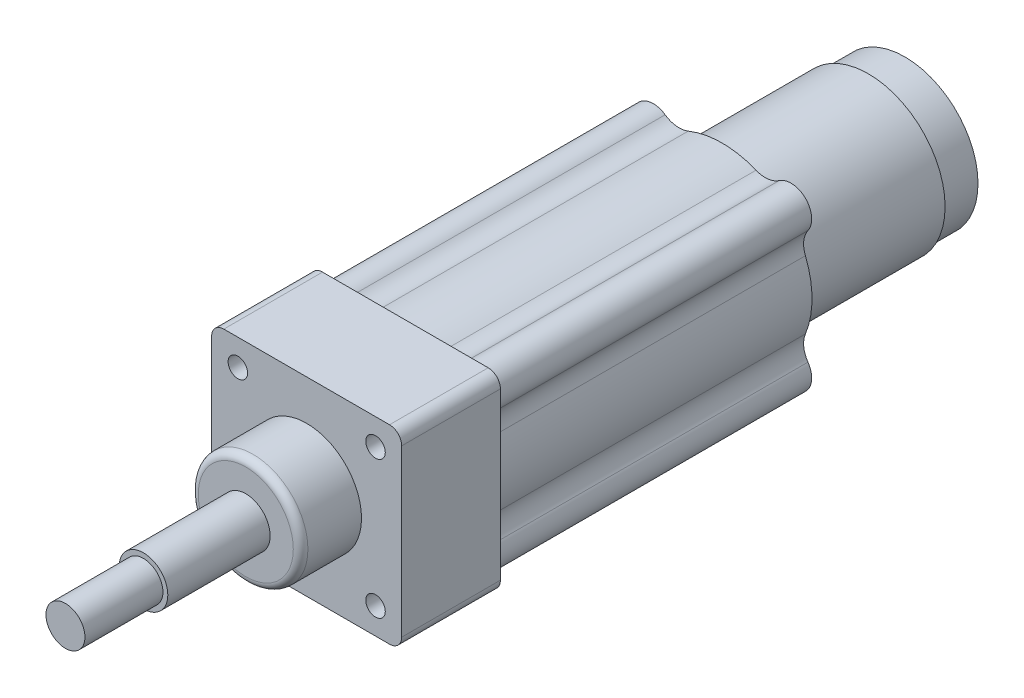
SolidWorks part; units mm, degrees
ref_plane "Alzado" through (0, 0, 0) normal (0, 0, 1) x (1, 0, 0)
ref_plane "Planta" through (0, 0, 0) normal (0, 1, 0) x (1, 0, 0)
ref_plane "Vista lateral" through (0, 0, 0) normal (1, 0, 0) x (0, 0, -1)
sketch "Croquis1" plane through (0, 0, 0) normal (0, 0, 1) x (1, 0, 0)
  line L1 (-34, -39) -> (34, -39)
  line L2 (-39, -34) -> (-39, 34)
  line L3 (-34, 39) -> (34, 39)
  line L4 (39, -34) -> (39, 34)
  line L5 (-39, -39) -> (39, 39) construction
  line L6 (-39, 39) -> (39, -39) construction
  arc A0 (34, -39) -> (39, -34) centre (34, -34) ccw
  arc A1 (-34, -39) -> (-39, -34) centre (-34, -34) cw
  arc A2 (-39, 34) -> (-34, 39) centre (-34, 34) cw
  arc A3 (34, 39) -> (39, 34) centre (34, 34) cw
  point P0 (0, 0)
  dimension "D3" = 5
  dimension "D1" = 78
  dimension "D2" = 78
extrude "Saliente-Extruir1" add sketch "Croquis1" against normal blind 40.5
sketch "Croquis2" plane through (0, 0, 0) normal (0, 0, 1) x (1, 0, 0)
  circle A0 centre (0, 0) radius 36.8862
extrude "Saliente-Extruir2" add sketch "Croquis2" against normal blind 170.5
sketch "Croquis3" plane through (0, 0, 0) normal (0, 0, 1) x (1, 0, 0)
  circle A0 centre (0, 0) radius 31.5
  dimension "D1" = 63
extrude "Saliente-Extruir3" add sketch "Croquis3" against normal blind 230.5
sketch "Croquis4" plane through (0, 0, -230.5) normal (0, 0, -1) x (-1, 0, 0)
  circle A0 centre (0, 0) radius 30
  dimension "D1" = 60
extrude "Saliente-Extruir4" add sketch "Croquis4" along normal blind 15
sketch "Croquis5" plane through (0, 0, 0) normal (0, 0, 1) x (1, 0, 0)
  line L1 (-28.25, -28.25) -> (28.25, -28.25) construction
  line L2 (-28.25, -28.25) -> (-28.25, 28.25) construction
  line L3 (-28.25, 28.25) -> (28.25, 28.25) construction
  line L4 (28.25, -28.25) -> (28.25, 28.25) construction
  line L5 (-28.25, -28.25) -> (28.25, 28.25) construction
  line L6 (-28.25, 28.25) -> (28.25, -28.25) construction
  circle A0 centre (28.25, 28.25) radius 8.5
  circle A1 centre (28.25, -28.25) radius 8.5
  circle A2 centre (-28.25, -28.25) radius 8.5
  circle A3 centre (-28.25, 28.25) radius 8.5
  point P8 (0, 0)
  dimension "D3" = 17
  dimension "D1" = 56.5
  dimension "D2" = 56.5
extrude "Saliente-Extruir5" add sketch "Croquis5" against normal blind 170.5
fillet "Redondeo2" radius 10 2 edges at (-20.1684, 30.884, -105.5) (20.1684, 30.884, -105.5)
fillet "Redondeo3" radius 10 2 edges at (-30.884, -20.1684, -105.5) (-30.884, 20.1684, -105.5)
fillet "Redondeo4" radius 10 2 edges at (20.1684, -30.884, -105.5) (-20.1684, -30.884, -105.5)
fillet "Redondeo5" radius 10 2 edges at (30.884, 20.1684, -105.5) (30.884, -20.1684, -105.5)
sketch "Croquis6" plane through (0, 0, 0) normal (0, 0, 1) x (1, 0, 0)
  line L1 (-28.25, -28.25) -> (28.25, -28.25) construction
  line L2 (-28.25, -28.25) -> (-28.25, 28.25) construction
  line L3 (-28.25, 28.25) -> (28.25, 28.25) construction
  line L4 (28.25, -28.25) -> (28.25, 28.25) construction
  line L5 (-28.25, -28.25) -> (28.25, 28.25) construction
  line L6 (-28.25, 28.25) -> (28.25, -28.25) construction
  circle A0 centre (28.25, 28.25) radius 4
  circle A1 centre (-28.25, 28.25) radius 4
  circle A2 centre (28.25, -28.25) radius 4
  circle A3 centre (-28.25, -28.25) radius 4
  point P0 (0, 0)
  dimension "D3" = 8
  dimension "D1" = 56.5
  dimension "D2" = 56.5
extrude "Cortar-Extruir1" cut sketch "Croquis6" against normal blind 17.5
sketch "Croquis7" plane through (0, 0, 0) normal (0, 0, 1) x (1, 0, 0)
  circle A0 centre (0, 0) radius 22.5
  dimension "D1" = 45
extrude "Saliente-Extruir7" add sketch "Croquis7" along normal blind 25
fillet "Redondeo6" radius 3 1 edges at (22.5, 0, 25)
sketch "Croquis8" plane through (0, 0, 25) normal (0, 0, 1) x (1, 0, 0)
  circle A0 centre (0, 0) radius 10
  dimension "D1" = 20
extrude "Saliente-Extruir8" add sketch "Croquis8" along normal blind 42
sketch "Croquis9" plane through (0, 0, 67) normal (0, 0, 1) x (1, 0, 0)
  circle A0 centre (0, 0) radius 8
  dimension "D1" = 16
extrude "Saliente-Extruir9" add sketch "Croquis9" along normal blind 32
